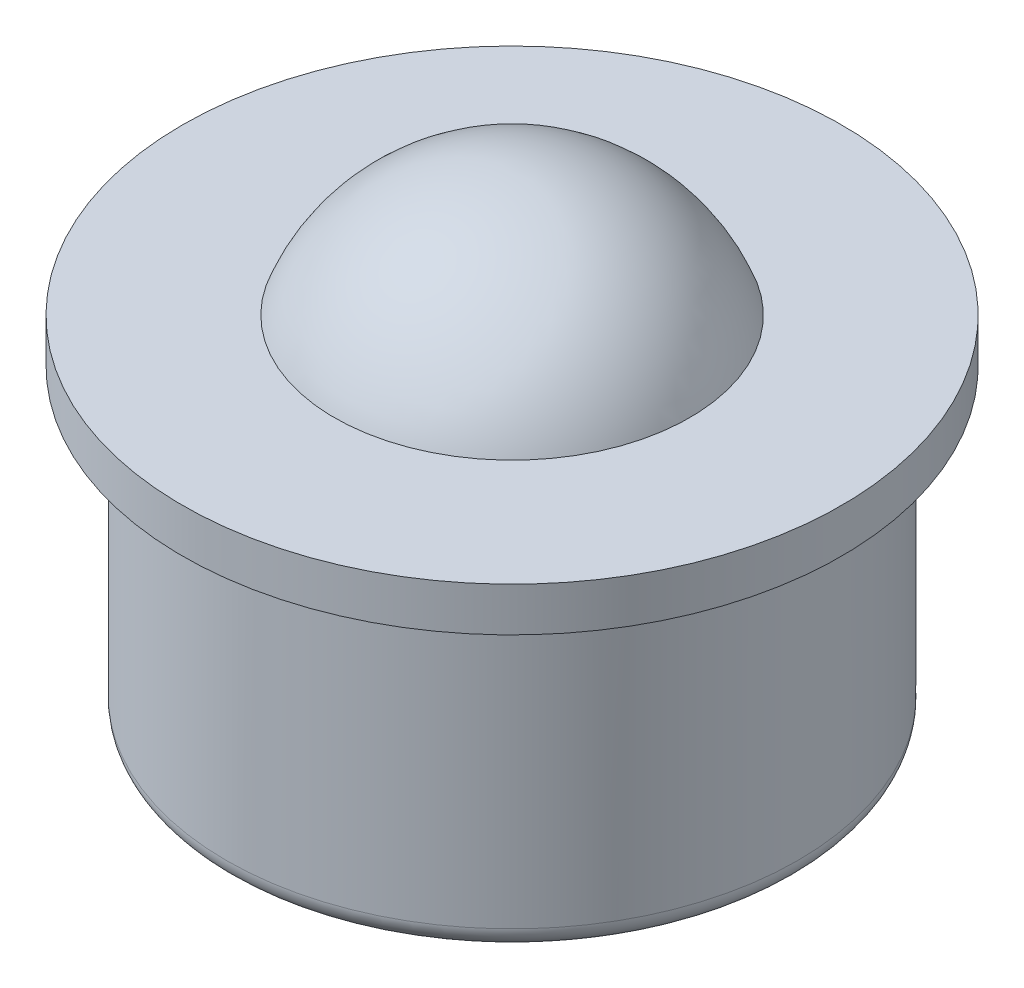
SolidWorks part; units mm, degrees
ref_plane "Front Plane" through (0, 0, 0) normal (0, 0, 1) x (1, 0, 0)
ref_plane "Top Plane" through (0, 0, 0) normal (0, 1, 0) x (1, 0, 0)
ref_plane "Right Plane" through (0, 0, 0) normal (1, 0, 0) x (0, 0, -1)
sketch "Sketch1" plane through (0, 0, 0) normal (0, 0, 1) x (1, 0, 0)
  line L0 (-6.5, 3.5) -> (-7.5, 3.5)
  line L1 (0, -3.5) -> (-6.5, -3.5)
  line L3 (0, 3.5) -> (-6.5, 3.5) construction
  line L4 (-6.5, -3.5) -> (-6.5, 3.5)
  line L5 (0, 0) -> (-6.5, 3.5) construction
  line L6 (0, 0) -> (-6.5, -3.5) construction
  line L7 (-7.5, 4.5) -> (-4.0438, 4.5)
  line L8 (-7.5, 4.5) -> (-7.5, 3.5)
  line L9 (-7.5, 3.5) -> (0, 3.5) construction
  line L12 (0, 7.3) -> (0, -3.5) construction
  line L14 (0, 7.3) -> (0, -3.5)
  arc A0 (0, 7.3) -> (-4.0438, 4.5) centre (0, 2.98) ccw
  point P0 (0, 0)
  point P12 (0, 7.3)
  dimension "D4" = 8.64
  dimension "D2" = 7
  dimension "D6" = 10.8
revolve "Revolve2" add sketch "Sketch1" angle 360 about L14
fillet "Fillet1" radius 0.5 1 edges at (-6.5, -3.5, 0)
